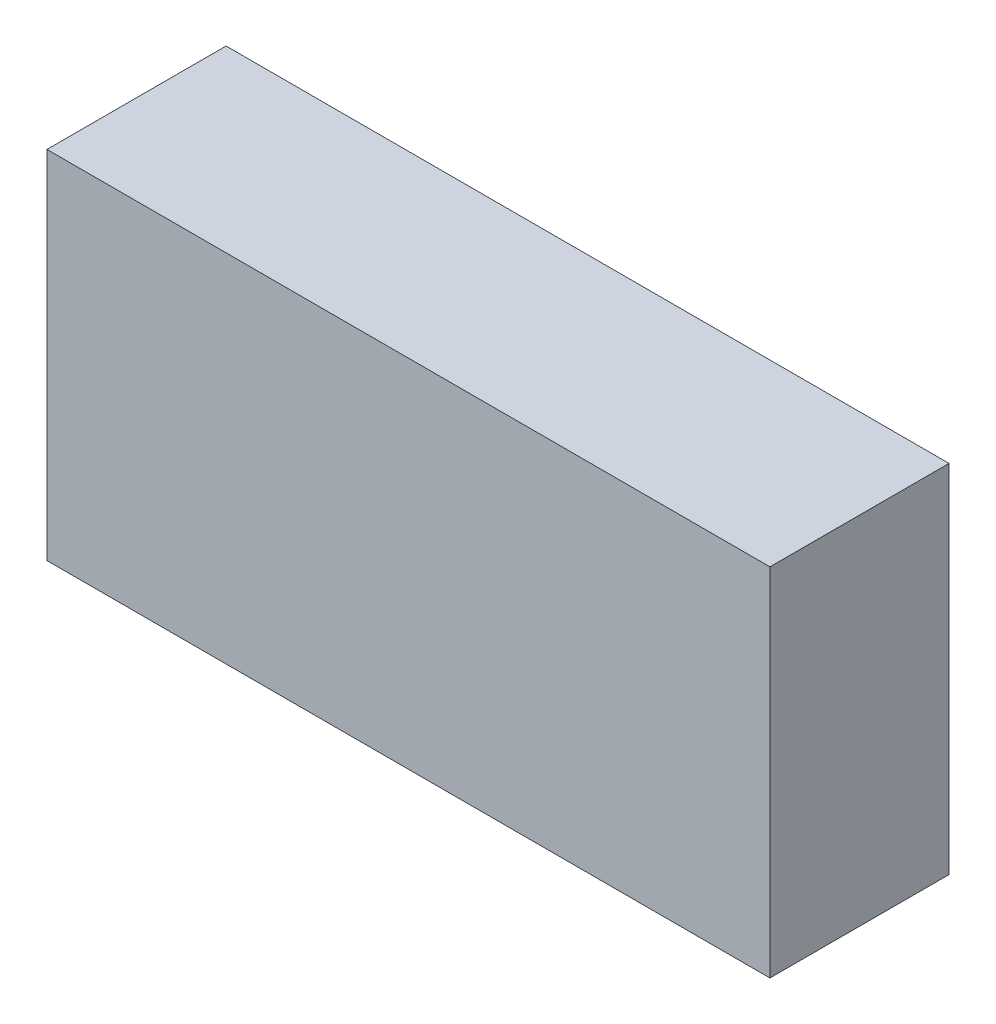
SolidWorks part; units mm, degrees
material "1060 Alloy"
ref_plane "Front Plane" through (0, 0, 0) normal (0, 0, 1) x (1, 0, 0)
ref_plane "Top Plane" through (0, 0, 0) normal (0, 1, 0) x (1, 0, 0)
ref_plane "Right Plane" through (0, 0, 0) normal (1, 0, 0) x (0, 0, -1)
sketch "Sketch1" plane through (0, 0, 0) normal (0, 0, 1) x (1, 0, 0)
  line L1 (0, 0) -> (85.09, 0)
  line L2 (0, 0) -> (0, 41.91)
  line L3 (0, 41.91) -> (85.09, 41.91)
  line L4 (85.09, 0) -> (85.09, 41.91)
  dimension "D1" = 41.91
  dimension "D2" = 85.09
extrude "Boss-Extrude1" add sketch "Sketch1" along normal blind 21.082
